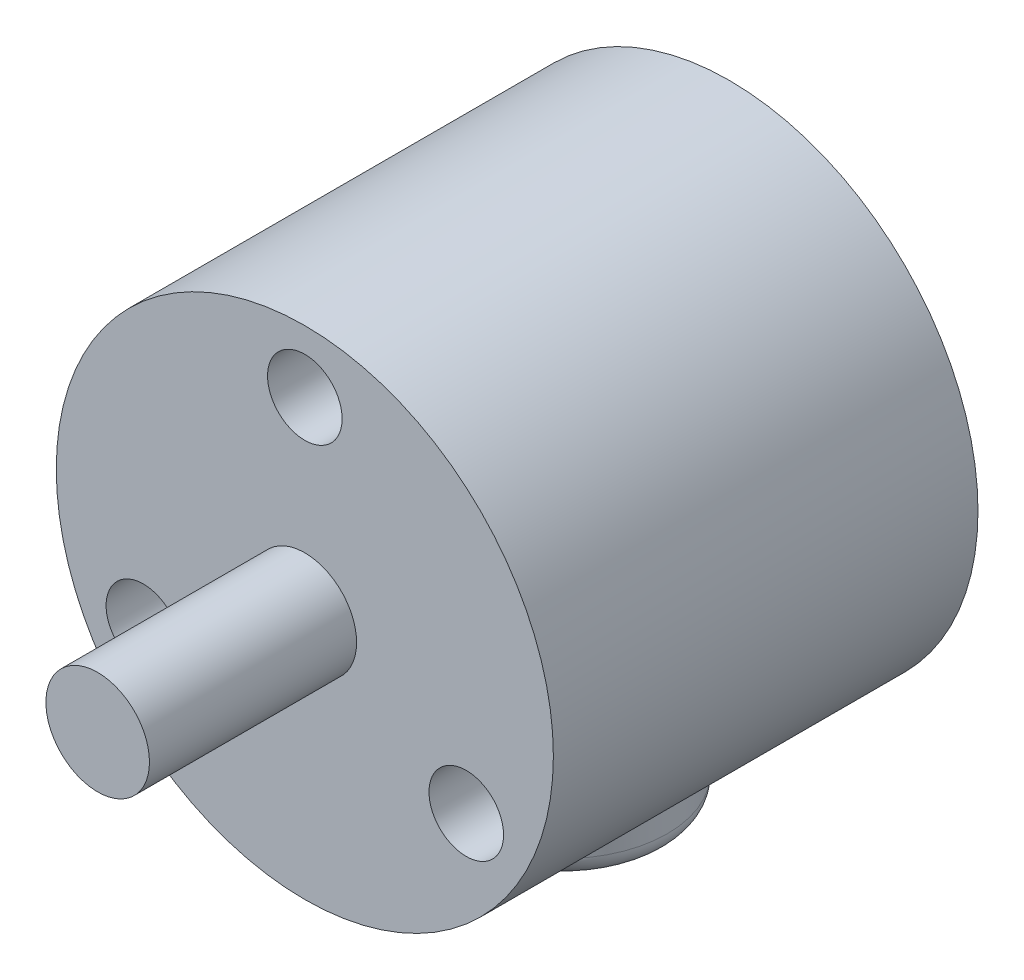
SolidWorks part; units mm, degrees
ref_plane "Plan de face" through (0, 0, 0) normal (0, 0, 1) x (1, 0, 0)
ref_plane "Plan de dessus" through (0, 0, 0) normal (0, 1, 0) x (1, 0, 0)
ref_plane "Plan de droite" through (0, 0, 0) normal (1, 0, 0) x (0, 0, -1)
sketch "Esquisse1" plane through (0, 0, 0) normal (0, 0, 1) x (1, 0, 0)
  circle A0 centre (0, 0) radius 12
  dimension "D1" = 24
extrude "Boss.-Extru.1" add sketch "Esquisse1" along normal blind 20.5
sketch "Esquisse2" plane through (0, 0, 20.5) normal (0, 0, 1) x (1, 0, 0)
  circle A0 centre (0, 0) radius 2.5
  dimension "D1" = 5
extrude "Boss.-Extru.2" add sketch "Esquisse2" along normal blind 3.5
sketch "Esquisse3" plane through (0, 0, 20.5) normal (0, 0, 1) x (1, 0, 0)
  line L0 (0, 0) -> (0, 9) construction
  line L1 (0, 0) -> (-7.7942, -4.5)
  line L2 (0, 0) -> (7.7942, -4.5)
  circle A0 centre (0, 0) radius 9 construction
  circle A1 centre (0, 9) radius 1.8
  circle A2 centre (-7.7942, -4.5) radius 1.8
  circle A3 centre (7.7942, -4.5) radius 1.8
  dimension "D1" = 120
  dimension "D2" = 120
  dimension "D3" = 9
extrude "Enlèv. mat.-Extru.1" cut sketch "Esquisse3" against normal blind 3
sketch "Esquisse4" plane through (0, 0, 24) normal (0, 0, 1) x (1, 0, 0)
  circle A0 centre (0, 0) radius 2.5
extrude "Boss.-Extru.3" add sketch "Esquisse4" along normal blind 6.5
sketch "Esquisse5" plane through (0, 0, 0) normal (0, 1, 0) x (1, 0, 0)
  line L0 (0, -8) -> (0, 0) construction
  circle A0 centre (0, -8) radius 5
extrude "Boss.-Extru.4" add sketch "Esquisse5" against normal blind 14
fillet "Congé1" radius 1 1 edges at (0, -14, 13)
